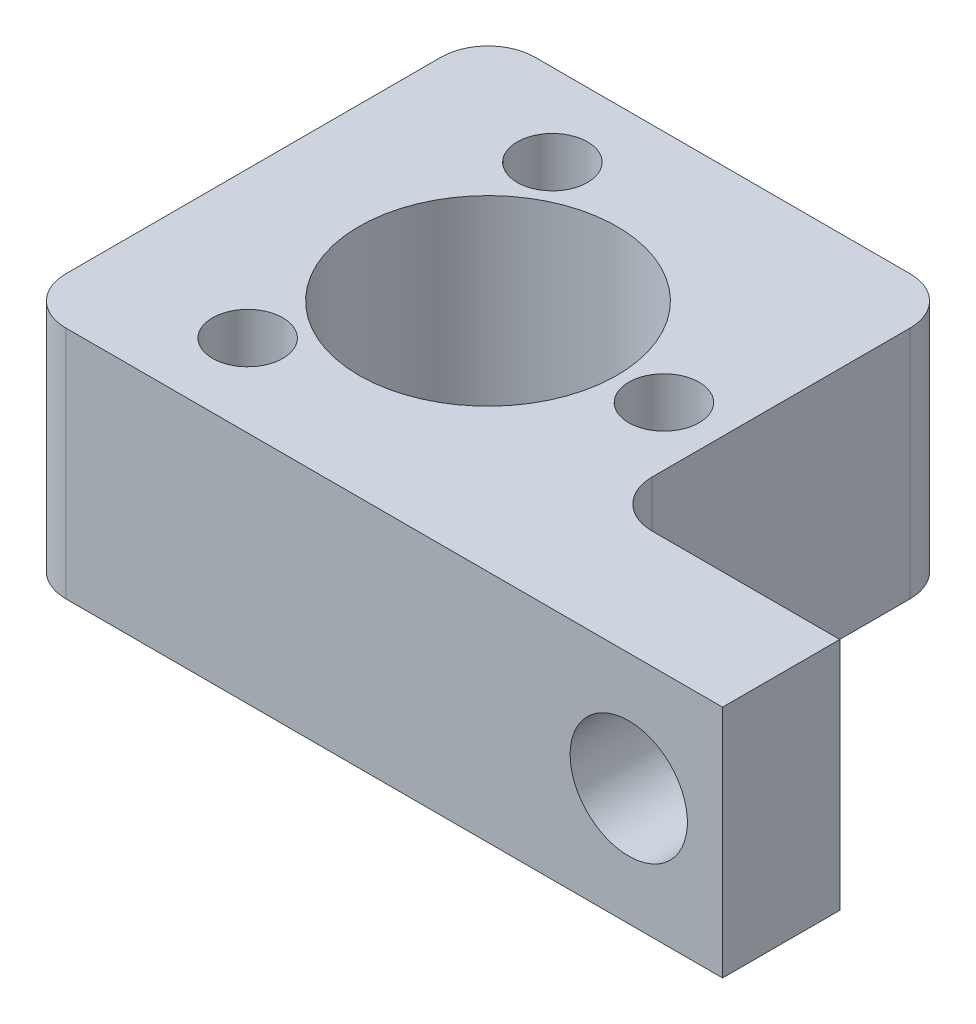
SolidWorks part; units mm, degrees
ref_plane "Front Plane" through (0, 0, 0) normal (0, 0, 1) x (1, 0, 0)
ref_plane "Top Plane" through (0, 0, 0) normal (0, 1, 0) x (1, 0, 0)
ref_plane "Right Plane" through (0, 0, 0) normal (1, 0, 0) x (0, 0, -1)
sketch "Sketch1" plane through (0, 0, 0) normal (0, 1, 0) x (1, 0, 0)
  line L1 (0, 0) -> (-25.4, 0)
  line L2 (0, 0) -> (0, 25.4)
  line L3 (0, 25.4) -> (-25.4, 25.4)
  line L4 (-25.4, 0) -> (-25.4, 25.4)
  line L5 (0, 6.35) -> (12.7, 6.35)
  line L6 (0, 6.35) -> (0, 0)
  line L7 (0, 0) -> (12.7, 0)
  line L8 (12.7, 6.35) -> (12.7, 0)
  circle A0 centre (-12.7, 12.7) radius 6.985
  circle A1 centre (-3.175, 12.7) radius 1.905
  circle A2 centre (-17.4625, 4.4511) radius 1.905
  circle A3 centre (-17.4625, 20.9489) radius 1.905
  dimension "D3" = 13.97
  dimension "D4" = 12.7
  dimension "D9" = 3.81
  dimension "D10" = 3.81
  dimension "D11" = 3.81
  dimension "D1" = 25.4
  dimension "D2" = 25.4
  dimension "D5" = 12.7
  dimension "D6" = 12.7
  dimension "D7" = 0
  dimension "D8" = 6.35
extrude "Boss-Extrude1" add sketch "Sketch1" along normal blind 12.7 contours L8 L5 L2 L7 | A0 | A1 | A2 | A3
fillet "Fillet1" radius 2.54 4 edges at (0, 6.35, -6.35) (-25.4, 6.35, 0) (-25.4, 6.35, -25.4) (0, 6.35, -25.4)
sketch "Sketch2" plane through (0, 0, -6.35) normal (0, 0, -1) x (-1, 0, 0)
  line L0 (-12.7, 12.7) -> (-12.7, 0) construction
  line L1 (-2.54, 0) -> (-12.7, 0) construction
  circle A0 centre (-7.62, 6.35) radius 3.175
  dimension "D1" = 6.35
  dimension "D2" = 5.08
  dimension "D3" = 6.35
extrude "Cut-Extrude1" cut sketch "Sketch2" against normal through all
